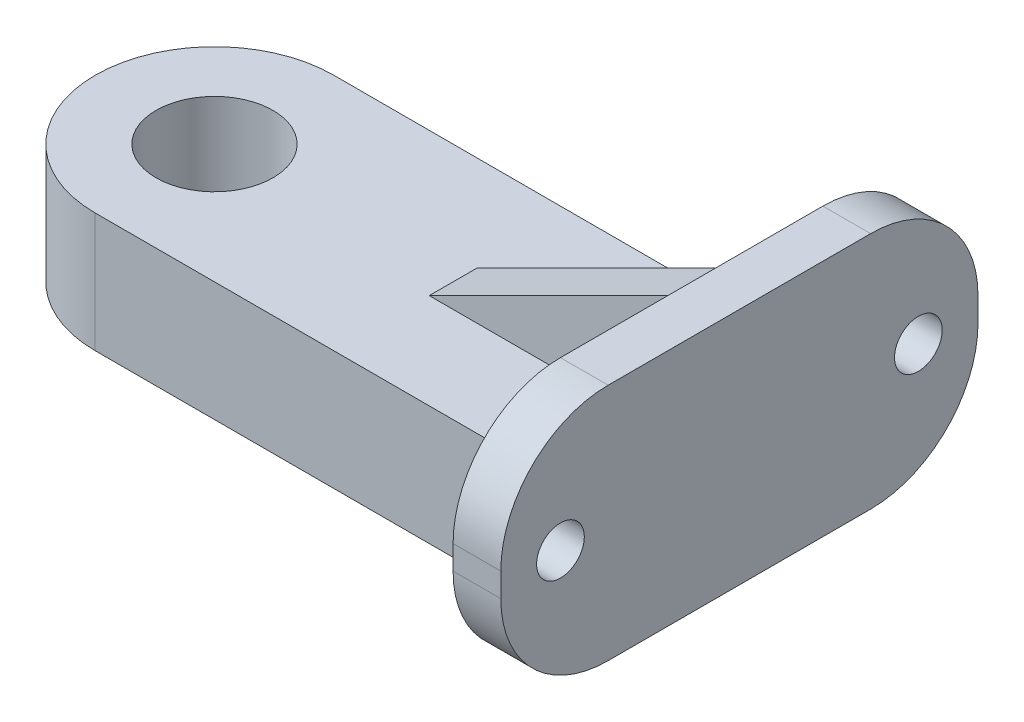
SolidWorks part; units mm, degrees
ref_plane "Front Plane" through (0, 0, 0) normal (0, 0, 1) x (1, 0, 0)
ref_plane "Top Plane" through (0, 0, 0) normal (0, 1, 0) x (1, 0, 0)
ref_plane "Right Plane" through (0, 0, 0) normal (1, 0, 0) x (0, 0, -1)
sketch "Sketch1" plane through (0, 0, 0) normal (0, 1, 0) x (1, 0, 0)
  line L0 (0, 0) -> (20, 0) construction
  line L1 (0, 5) -> (20, 5)
  line L2 (0, -5) -> (20, -5)
  line L3 (20, 5) -> (20, -5)
  arc A0 (0, 5) -> (0, -5) centre (0, 0) ccw
  circle A2 centre (0, 0) radius 2.45
  point P3 (10, 0)
  dimension "D1" = 4.9
  dimension "D5" = 5
  dimension "D2" = 10
  dimension "D3" = 20
  dimension "D4" = 20
  dimension "D6" = 20
extrude "Boss-Extrude1" add sketch "Sketch1" along normal blind 5
sketch "Sketch2" plane through (20, 0, 0) normal (1, 0, 0) x (0, 0, -1)
  line L1 (-5.5, 10) -> (5.5, 10)
  line L2 (-10, 5.5) -> (-10, 4.5)
  line L3 (-5.5, 0) -> (5.5, 0)
  line L4 (10, 5.5) -> (10, 4.5)
  line L5 (-10, 10) -> (10, 0) construction
  line L6 (-10, 0) -> (10, 10) construction
  arc A0 (5.5, 0) -> (10, 4.5) centre (5.5, 4.5) ccw
  arc A1 (5.5, 10) -> (10, 5.5) centre (5.5, 5.5) cw
  arc A2 (-5.5, 10) -> (-10, 5.5) centre (-5.5, 5.5) ccw
  arc A3 (-10, 4.5) -> (-5.5, 0) centre (-5.5, 4.5) ccw
  circle A4 centre (-7.5, 5) radius 1
  circle A5 centre (7.5, 5) radius 1
  point P0 (0, 5)
  dimension "D4" = 4.5
  dimension "D5" = 2
  dimension "D6" = 2
  dimension "D1" = 20
  dimension "D2" = 10
  dimension "D3" = 10
  dimension "D7" = 15
  dimension "D8" = 7.5
  dimension "D9" = 5
  dimension "D10" = 5
extrude "Boss-Extrude2" add sketch "Sketch2" along normal blind 2
ref_plane "Plane1" through (0, 0, 0) normal (0, 0, 1) x (1, 0, 0)
sketch "Sketch3" plane through (0, 0, 0) normal (0, 0, 1) x (1, 0, 0)
  line L0 (10, 5) -> (20, 10)
  line L1 (0, 5) -> (20, 5) construction
  line L2 (20, 10) -> (20, 5)
  line L3 (20, 5.5) -> (20, 4.5) construction
  line L4 (20, 5) -> (10, 5)
extrude "Boss-Extrude3" add sketch "Sketch3" along normal mid plane 2
